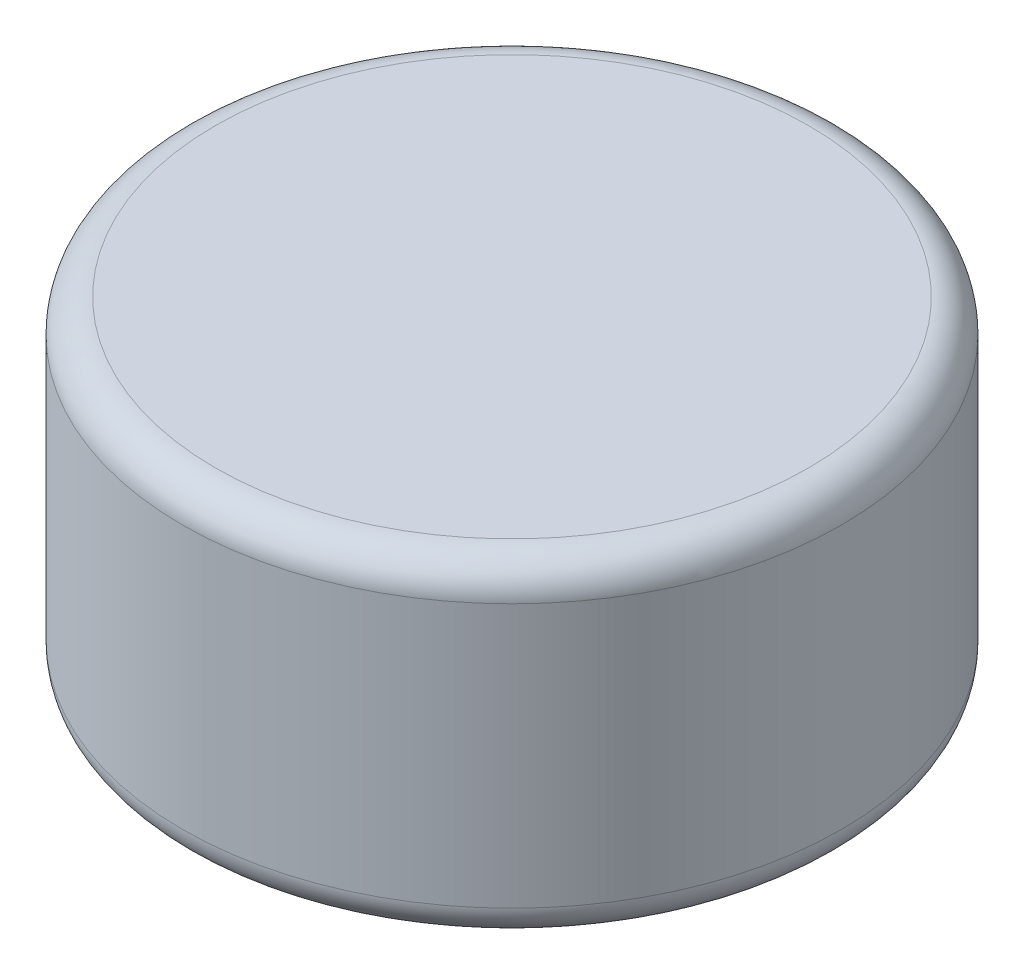
SolidWorks part; units mm, degrees
ref_plane "Front Plane" through (0, 0, 0) normal (0, 0, 1) x (1, 0, 0)
ref_plane "Top Plane" through (0, 0, 0) normal (0, 1, 0) x (1, 0, 0)
ref_plane "Right Plane" through (0, 0, 0) normal (1, 0, 0) x (0, 0, -1)
sketch "Sketch1" plane through (0, 0, 0) normal (0, 1, 0) x (1, 0, 0)
  circle A0 centre (0, 0) radius 3.175
  dimension "OD" = 6.35
extrude "Boss-Extrude1" add sketch "Sketch1" along normal mid plane 3.175
fillet "Fillet1" radius 0.3175 2 edges at (0, -1.5875, 3.175) (0, 1.5875, 3.175)
equation "\"D1@Fillet1\"=\"Thickness@Boss-Extrude1\"/10"
